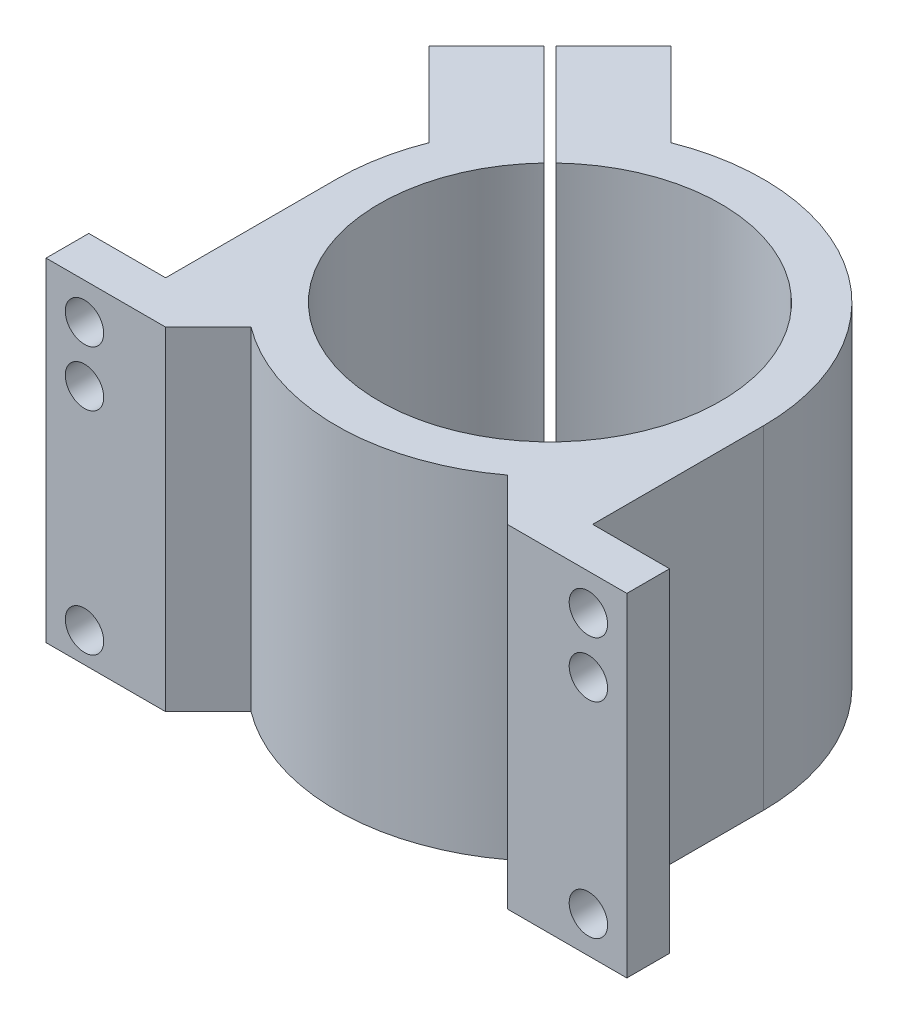
SolidWorks part; units mm, degrees
ref_plane "Front Plane" through (0, 0, 0) normal (0, 0, 1) x (1, 0, 0)
ref_plane "Top Plane" through (0, 0, 0) normal (0, 1, 0) x (1, 0, 0)
ref_plane "Right Plane" through (0, 0, 0) normal (1, 0, 0) x (0, 0, -1)
sketch "Sketch1" plane through (0, 0, 0) normal (0, 1, 0) x (1, 0, 0)
  line L0 (-50, -50) -> (-40, -50)
  line L1 (-50, 0) -> (-50, -40)
  line L2 (50, 0) -> (50, -40)
  line L3 (-50, -50) -> (-68, -50)
  line L4 (-68, -50) -> (-68, -40)
  line L5 (-68, -40) -> (-50, -40)
  line L6 (-40, -50) -> (-30, -40)
  line L7 (0, 50) -> (0, -50) construction
  line L8 (40, -50) -> (30, -40)
  line L9 (68, -40) -> (50, -40)
  line L10 (68, -50) -> (68, -40)
  line L11 (50, -50) -> (68, -50)
  line L12 (50, 0) -> (50, -40)
  line L13 (50, -50) -> (40, -50)
  line L14 (0, 0) -> (-52.0069, 52.0069) construction
  line L15 (-66.149, 37.8647) -> (-52.714, 51.2998)
  line L16 (-66.149, 37.8647) -> (-46.5458, 18.2616)
  line L17 (-37.8647, 66.149) -> (-18.2616, 46.5458)
  line L18 (-51.2998, 52.714) -> (-27.5683, 28.9825)
  line L19 (-52.714, 51.2998) -> (-28.9825, 27.5683)
  line L20 (-51.2998, 52.714) -> (-37.8647, 66.149)
  circle A0 centre (0, 0) radius 40
  arc A1 (-30, -40) -> (30, -40) centre (0, 0) ccw
  arc A2 (50, 0) -> (-18.2616, 46.5458) centre (0, 0) ccw
  arc A3 (-46.5458, 18.2616) -> (-50, 0) centre (0, 0) ccw
  dimension "D1" = 80
  dimension "D2" = 100
  dimension "D3" = 10
  dimension "18" = 18
  dimension "D4" = 45
  dimension "D5" = 10
  dimension "D6" = 45
  dimension "D7" = 40
  dimension "D8" = 1
  dimension "D9" = 1
extrude "Boss-Extrude2" add sketch "Sketch1" along normal blind 78 contours L16 A3 L1 L5 L4 L3 L0 L6 A1 L8 L13 L11 L10 L9 L2 A2 L17 L20 L18 A0 L19 L15
hole_wizard "M8 Clearance Hole1" positions "Sketch2" profile "Sketch3" hole size "M8" standard "ISO"
sketch "Sketch2" plane through (0, 0, 50) normal (0, 0, 1) x (1, 0, 0)
  line L1 (30, 78) -> (-30, 78) construction
  line L3 (0, 0) -> (0, 78) construction
  line L4 (-30, 0) -> (30, 0) construction
  line L6 (-68, 78) -> (-68, 0) construction
  line L7 (-40, 0) -> (-68, 0) construction
  line L8 (-40, 78) -> (-68, 78) construction
  line L9 (68, 0) -> (50, 0) construction
  line L10 (68, 78) -> (68, 0) construction
  point P0 (-59, 69.5)
  point P2 (-59, 7)
  point P22 (-59, 56.5)
  point P29 (59, 56.5)
  point P30 (59, 8.5)
  point P31 (59, 69.5)
  dimension "D1" = 9
  dimension "D2" = 7
  dimension "D3" = 8.5
  dimension "D4" = 13
  dimension "D5" = 8.5
  dimension "D6" = 9
sketch "Sketch3" plane through (-59, 69.5, 50) normal (1, 0, 0) x (0, -1, 0)
  line L0 (0, 0) -> (0, 12.7039)
  line L1 (0, 12.7039) -> (4.5, 10)
  line L2 (4.5, 10) -> (4.5, 0)
  line L5 (4.5, 0) -> (0, 0)
  line L10 (0, 12.7039) -> (-4.5, 10) construction
  line L11 (0, -6.35) -> (0, 107.95) construction
  dimension "Hole Dia." = 9
  dimension "Hole Depth" = 10
  dimension "Drill Angle" = 118
hole_wizard "M8 Clearance Hole2" positions "Sketch4" profile "Sketch5" hole size "M8" standard "ISO" end condition through all
sketch "Sketch4" plane through (14.1421, 0, -14.1421) normal (0.7071, 0, -0.7071) x (-0.7071, 0, -0.7071)
  line L0 (59.6873, 78) -> (59.6873, 0) construction
  line L1 (73.5488, 78) -> (45.8258, 78) construction
  line L2 (73.5488, 0) -> (45.8258, 0) construction
  point P0 (59.6873, 8.5)
  point P3 (59.6873, 69.5)
  dimension "D1" = 8.5
  dimension "D2" = 8.5
sketch "Sketch5" plane through (-28.0632, 8.5, -56.3474) normal (0, 1, 0) x (-0.7071, 0, -0.7071)
  line L0 (0, 0) -> (0, 103.4386)
  line L1 (0, 103.4386) -> (4.5, 103.4386)
  line L2 (4.5, 103.4386) -> (4.5, 0)
  line L5 (4.5, 0) -> (0, 0)
  line L11 (0, -6.35) -> (0, 107.95) construction
  dimension "Thru Hole Dia." = 9
  dimension "Thru Hole Depth" = 103.4386
